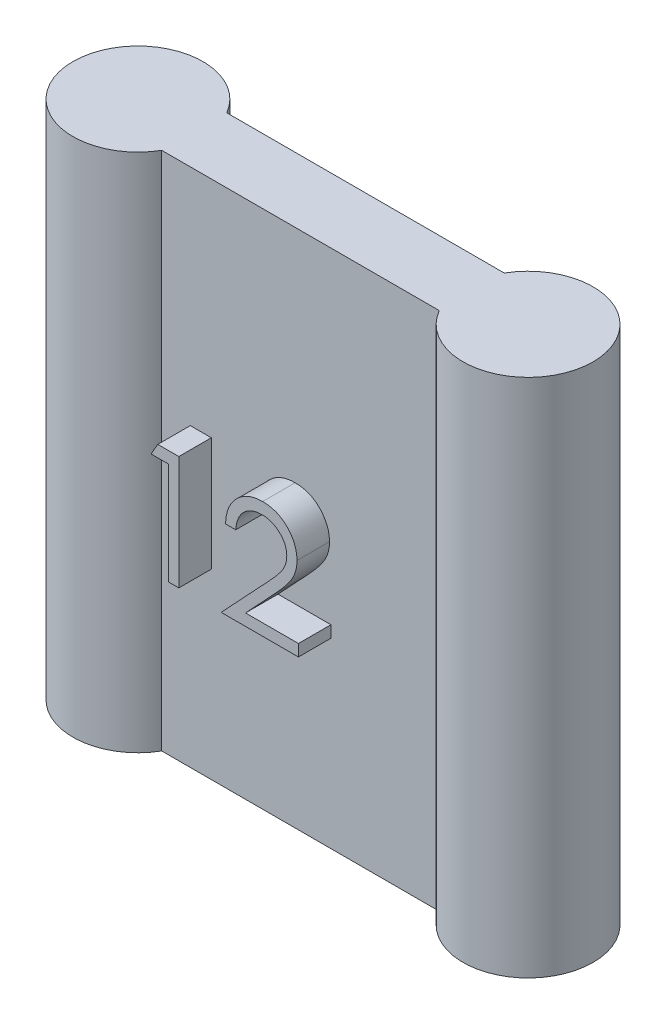
SolidWorks part; units mm, degrees
ref_plane "Front Plane" through (0, 0, 0) normal (0, 0, 1) x (1, 0, 0)
ref_plane "Top Plane" through (0, 0, 0) normal (0, 1, 0) x (1, 0, 0)
ref_plane "Right Plane" through (0, 0, 0) normal (1, 0, 0) x (0, 0, -1)
sketch "Sketch1" plane through (0, 0, 0) normal (0, 0, 1) x (1, 0, 0)
  line L1 (6, 8) -> (-6, 8)
  line L2 (6, 8) -> (6, -8)
  line L3 (6, -8) -> (-6, -8)
  line L4 (-6, 8) -> (-6, -8)
  line L5 (6, 8) -> (-6, -8) construction
  line L6 (6, -8) -> (-6, 8) construction
  point P1 (0, 0)
  dimension "D1" = 12
  dimension "16" = 16
extrude "Boss-Extrude1" add sketch "Sketch1" along normal blind 2
sketch "Sketch4" plane through (0, -8, 0) normal (0, -1, 0) x (1, 0, 0)
  line L0 (-6, 2) -> (-6, 0) construction
  line L1 (6, 2) -> (6, 0) construction
  circle A0 centre (-6, 1) radius 2
  circle A1 centre (6, 1) radius 2
  dimension "D1" = 4
  dimension "D2" = 4
extrude "Boss-Extrude4" add sketch "Sketch4" against normal up to surface (16 mm away) up to face at (0, 8, 1)
sketch "Sketch5" plane through (0, 0, 2) normal (0, 0, 1) x (1, 0, 0)
  line L0 (-4.2679, -2.3933) -> (4.2679, -2.3933) construction
  line L1 (-4.2679, 8) -> (-4.2679, -8) construction
  line L2 (4.2679, -8) -> (4.2679, 8) construction
  text T0 "12"
extrude "Boss-Extrude5" add sketch "Sketch5" along normal blind 1
